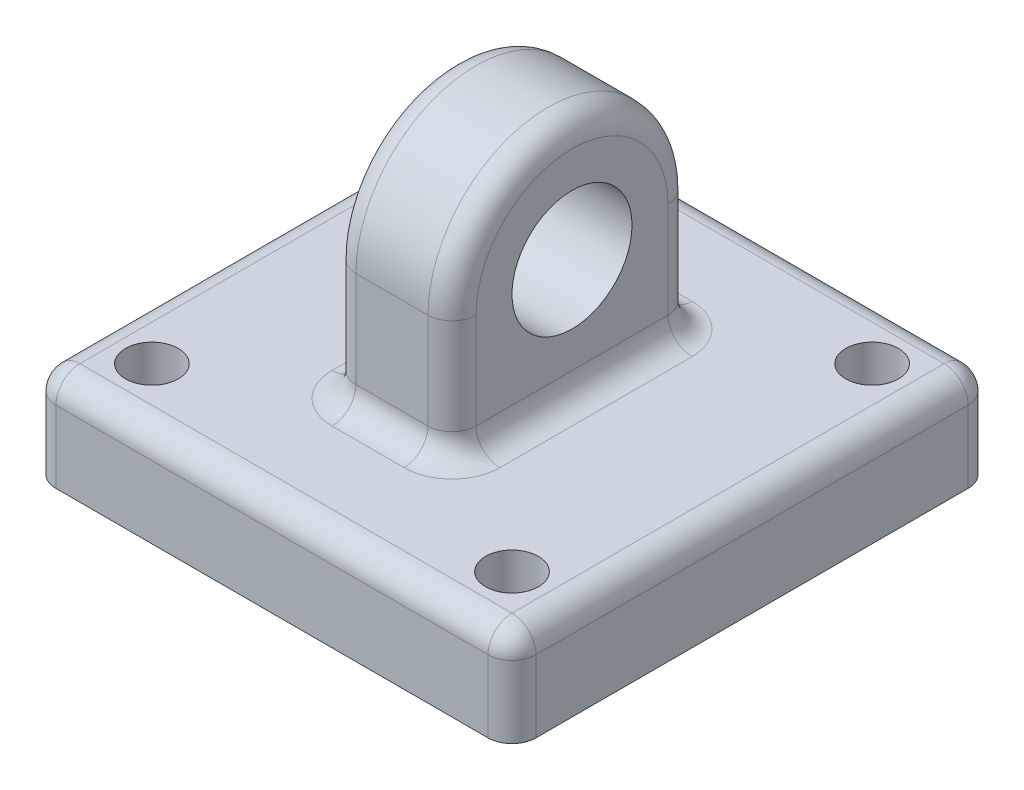
SolidWorks part; units mm, degrees
ref_plane "Plan de face" through (0, 0, 0) normal (0, 0, 1) x (1, 0, 0)
ref_plane "Plan de dessus" through (0, 0, 0) normal (0, 1, 0) x (1, 0, 0)
ref_plane "Plan de droite" through (0, 0, 0) normal (1, 0, 0) x (0, 0, -1)
sketch "Esquisse2" plane through (0, 0, 0) normal (1, 0, 0) x (0, 0, -1)
  line L0 (5, 0) -> (5, -5)
  line L2 (-5, 0) -> (-5, -5)
  line L3 (-5, -5) -> (5, -5)
  circle A0 centre (0, 0) radius 2.5
  arc A2 (5, 0) -> (-5, 0) centre (0, 0) ccw
  dimension "D1" = 5
  dimension "D2" = 5
  dimension "D3" = 5
  dimension "D4" = 5
extrude "Boss.-Extru.1" add sketch "Esquisse2" along normal mid plane 5
sketch "Esquisse4" plane through (0, -5, 0) normal (0, -1, 0) x (1, 0, 0)
  line L1 (-10, -10) -> (10, -10)
  line L2 (-10, -10) -> (-10, 10)
  line L3 (-10, 10) -> (10, 10)
  line L4 (10, -10) -> (10, 10)
  dimension "D1" = 20
  dimension "D2" = 20
  dimension "D3" = 10
  dimension "D4" = 10
extrude "Boss.-Extru.2" add sketch "Esquisse4" along normal blind 4
sketch "Esquisse5" plane through (0, -5, 0) normal (0, 1, 0) x (1, 0, 0)
  circle A0 centre (7.5, -7.5) radius 1.1
  circle A1 centre (7.5, 7.5) radius 1.1
  circle A2 centre (-7.5, 7.5) radius 1.1
  circle A3 centre (-7.5, -7.5) radius 1.1
  point P15 (0, 0)
  dimension "D1" = 2.2
  dimension "D2" = 15
  dimension "D3" = 15
  dimension "D4" = 7.5
  dimension "D5" = 7.5
extrude "Enlèv. mat.-Extru.1" cut sketch "Esquisse5" against normal up to next contours A0
fillet "Congé1" radius 1 18 edges at (10, -7, 10) (-10, -7, 10) (-10, -7, -10) (10, -7, -10) (0, -5, -10) (-10, -5, 0) (0, -5, 10) (10, -5, 0) (0, -5, -5) (2.5, -5, 0) (-2.5, -5, 0) (-2.5, -2.5, -5) (-2.5, 5, 0) (2.5, -2.5, -5) (2.5, 5, 0) (0, -5, 5) (-2.5, -2.5, 5) (2.5, -2.5, 5)
